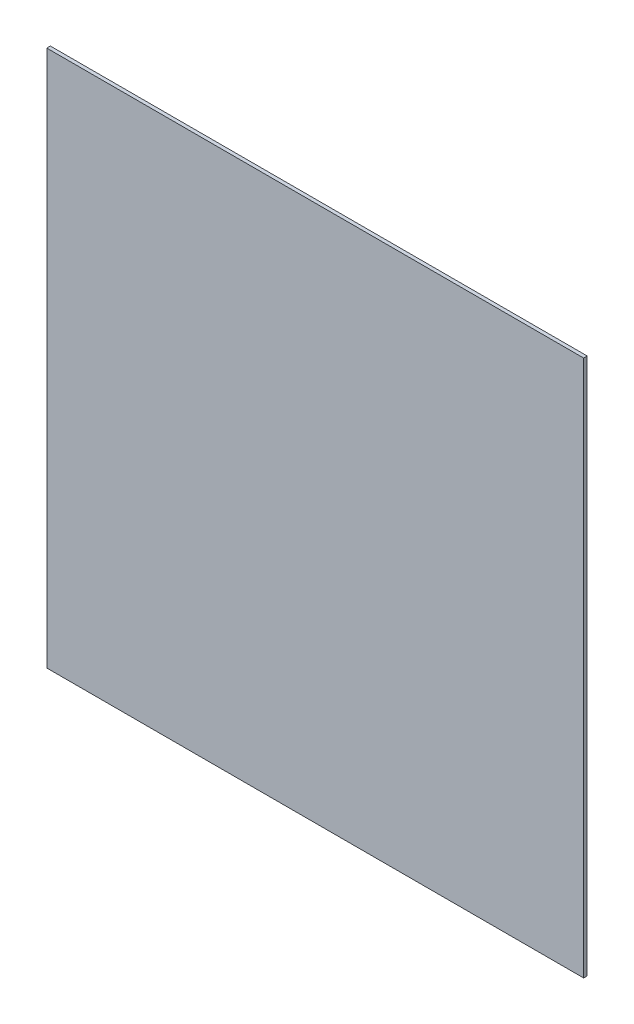
SolidWorks part; units mm, degrees
ref_plane "Front Plane" through (0, 0, 0) normal (0, 0, 1) x (1, 0, 0)
ref_plane "Top Plane" through (0, 0, 0) normal (0, 1, 0) x (1, 0, 0)
ref_plane "Right Plane" through (0, 0, 0) normal (1, 0, 0) x (0, 0, -1)
sketch "Model" plane through (0, 0, 0) normal (0, 0, 1) x (1, 0, 0)
  line L1 (-284.0096, 207.9676) -> (165.9904, 207.9676)
  line L2 (-284.0096, 207.9676) -> (-284.0096, -242.0324)
  line L3 (-284.0096, -242.0324) -> (165.9904, -242.0324)
  line L4 (165.9904, 207.9676) -> (165.9904, -242.0324)
  dimension "D1" = 450
  dimension "D2" = 450
extrude "Boss-Extrude1" add sketch "Model" along normal blind 3
